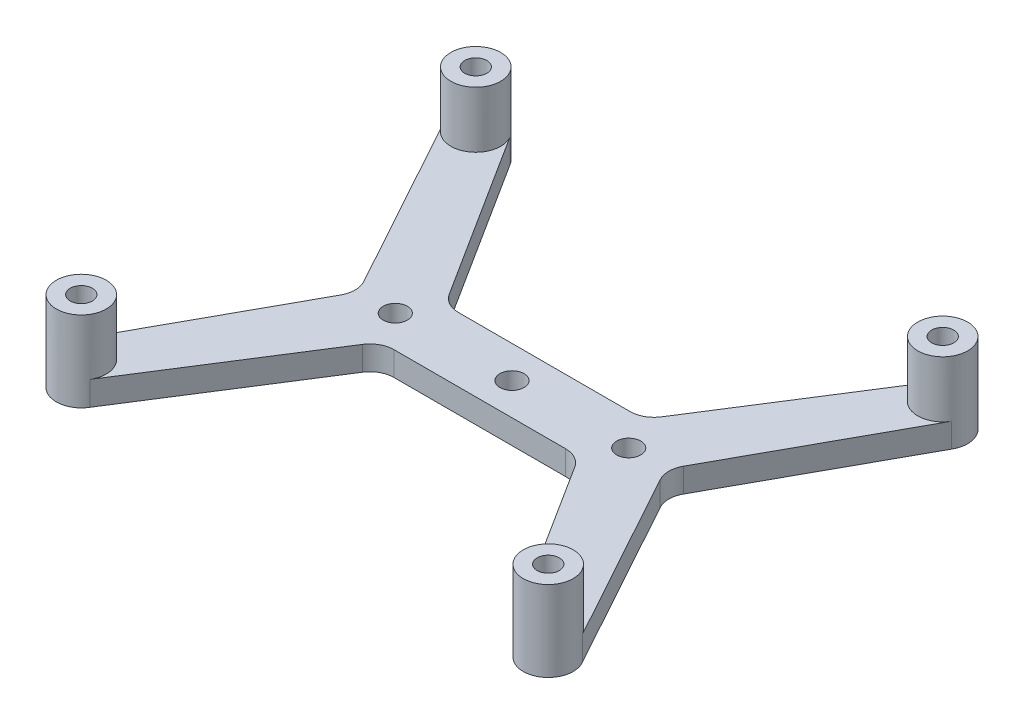
SolidWorks part; units mm, degrees
ref_plane "Front Plane" through (0, 0, 0) normal (0, 0, 1) x (1, 0, 0)
ref_plane "Top Plane" through (0, 0, 0) normal (0, 1, 0) x (1, 0, 0)
ref_plane "Right Plane" through (0, 0, 0) normal (1, 0, 0) x (0, 0, -1)
sketch "Sketch1" plane through (0, 0, 0) normal (0, 1, 0) x (1, 0, 0)
  line L0 (0, 49) -> (58, 0) construction
  line L1 (0, 0) -> (58, 0) construction
  line L2 (0, 0) -> (0, 49) construction
  line L3 (0, 49) -> (58, 49) construction
  line L4 (58, 0) -> (58, 49) construction
  line L5 (0, 0) -> (58, 49) construction
  line L6 (29, 24.5) -> (14.5, 24.5) construction
  line L7 (29, 24.5) -> (43.5, 24.5) construction
  line L8 (14.5, 28.5) -> (29, 28.5)
  line L9 (29, 28.5) -> (43.5, 28.5)
  line L10 (14.5, 20.5) -> (29, 20.5)
  line L11 (29, 20.5) -> (43.5, 20.5)
  line L12 (14.5, 24.5) -> (0, 49) construction
  line L13 (43.5, 24.5) -> (58, 49) construction
  line L14 (14.5, 24.5) -> (0, 0) construction
  line L15 (43.5, 24.5) -> (58, 0) construction
  line L16 (0, 49) -> (2.6678, 50.5789) construction
  line L17 (0, 49) -> (-2.6678, 47.4211) construction
  line L18 (14.5, 24.5) -> (17.9423, 26.5373) construction
  line L19 (14.5, 24.5) -> (11.0577, 22.4627) construction
  line L20 (14.5, 24.5) -> (17.9423, 22.4627) construction
  line L21 (14.5, 24.5) -> (11.0577, 26.5373) construction
  line L22 (11.0577, 22.4627) -> (-2.6678, 47.4211)
  line L23 (2.6678, 50.5789) -> (17.9423, 26.5373)
  line L24 (0, 0) -> (-2.6678, 1.5789) construction
  line L25 (0, 0) -> (2.6678, -1.5789) construction
  line L26 (58, 0) -> (55.3322, -1.5789) construction
  line L27 (58, 0) -> (60.6678, 1.5789) construction
  line L28 (58, 49) -> (55.3322, 50.5789) construction
  line L29 (58, 49) -> (60.6678, 47.4211) construction
  line L30 (43.5, 24.5) -> (40.0577, 26.5373) construction
  line L31 (43.5, 24.5) -> (46.9423, 22.4627) construction
  line L32 (43.5, 24.5) -> (40.0577, 22.4627) construction
  line L33 (43.5, 24.5) -> (46.9423, 26.5373) construction
  line L34 (11.0577, 26.5373) -> (-2.6678, 1.5789)
  line L35 (17.9423, 22.4627) -> (2.6678, -1.5789)
  line L36 (40.0577, 22.4627) -> (55.3322, -1.5789)
  line L37 (46.9423, 26.5373) -> (60.6678, 1.5789)
  line L38 (40.0577, 26.5373) -> (55.3322, 50.5789)
  line L39 (46.9423, 22.4627) -> (60.6678, 47.4211)
  circle A0 centre (0, 49) radius 1.375
  circle A1 centre (0, 49) radius 3.1
  circle A2 centre (0, 0) radius 1.375
  circle A3 centre (0, 0) radius 3.1
  circle A4 centre (58, 0) radius 1.375
  circle A5 centre (58, 0) radius 3.1
  circle A6 centre (58, 49) radius 1.375
  circle A7 centre (58, 49) radius 3.1
  circle A8 centre (14.5, 24.5) radius 1.5
  circle A9 centre (14.5, 24.5) radius 4
  circle A10 centre (29, 24.5) radius 1.5
  circle A11 centre (29, 24.5) radius 4
  circle A12 centre (43.5, 24.5) radius 1.5
  circle A13 centre (43.5, 24.5) radius 4
  dimension "D3" = 2.75
  dimension "D4" = 6.2
  dimension "D5" = 2.75
  dimension "D6" = 6.2
  dimension "D7" = 2.75
  dimension "D8" = 6.2
  dimension "D9" = 2.75
  dimension "D10" = 6.2
  dimension "D13" = 3
  dimension "D14" = 8
  dimension "D15" = 3
  dimension "D16" = 8
  dimension "D17" = 3
  dimension "D18" = 8
  dimension "D1" = 58
  dimension "D2" = 49
  dimension "D11" = 14.5
  dimension "D12" = 14.5
extrude "Boss-Extrude1" add sketch "Sketch1" along normal blind 3 contours A9 L34 L22 | A9 L23 L8 | A9 L10 L35 | A9 L35 L23 L34 L22 A8 | A11 L8 L23 A9 L35 L10 | A11 A10 | A13 L38 L9 A11 L11 L36 | A13 L36 L11 | A13 L9 L38 | A13 L39 L37 | A13 L39 L37 L38 L36 A12 | A13 L11 L36 A5 L37 L39 | A13 L37 L39 A7 L38 L9 | A9 L22 L34 A3 L35 L10 | A3 A2 | A1 A0 | A9 L8 L23 A1 L22 L34 | A7 A6 | A5 A4
sketch "Sketch2" plane through (0, 3, 0) normal (0, 1, 0) x (1, 0, 0)
  circle A0 centre (0, 49) radius 3.1
  circle A1 centre (0, 49) radius 1.375
  circle A2 centre (58, 49) radius 1.375
  circle A3 centre (58, 49) radius 3.1
  circle A4 centre (58, 0) radius 1.375
  circle A5 centre (58, 0) radius 3.1
  circle A6 centre (0, 0) radius 1.375
  circle A7 centre (0, 0) radius 3.1
extrude "Boss-Extrude2" add sketch "Sketch2" along normal blind 7
fillet "Fillet4" radius 3 6 edges at (9.9373, 1.5, -24.5) (16.6953, 1.5, -20.5) (41.3047, 1.5, -20.5) (48.0627, 1.5, -24.5) (41.3047, 1.5, -28.5) (16.6953, 1.5, -28.5)
